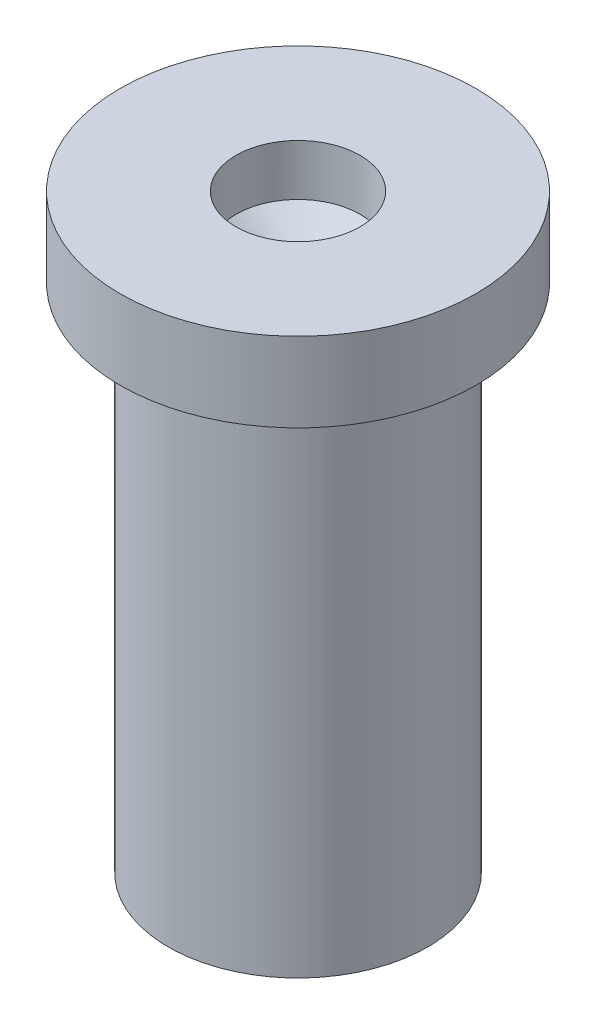
SolidWorks part; units mm, degrees
ref_plane "Front Plane" through (0, 0, 0) normal (0, 0, 1) x (1, 0, 0)
ref_plane "Top Plane" through (0, 0, 0) normal (0, 1, 0) x (1, 0, 0)
ref_plane "Right Plane" through (0, 0, 0) normal (1, 0, 0) x (0, 0, -1)
sketch "Sketch1" plane through (0, 0, 0) normal (0, 0, 1) x (1, 0, 0)
  line L0 (0, 0) -> (0, 11.8775) construction
  line L1 (0, 0) -> (3.1, 0)
  line L2 (3.1, 0) -> (3.1, 12.2)
  line L3 (3.1, 12.2) -> (4.2504, 12.2)
  line L4 (4.2504, 12.2) -> (4.2504, 14.0963)
  line L5 (4.2504, 14.0963) -> (1.4825, 14.0963)
  line L6 (1.4825, 14.0963) -> (1.4825, 12.8752)
  line L7 (0, 0) -> (0, 11.8775)
  line L8 (1.4825, 12.8752) -> (0, 11.8775)
  line L9 (0, 12.8752) -> (0, 19.8056) construction
  dimension "D1" = 6.2
  dimension "D2" = 12.2
revolve "Revolve1" add sketch "Sketch1" angle 360 about L0
